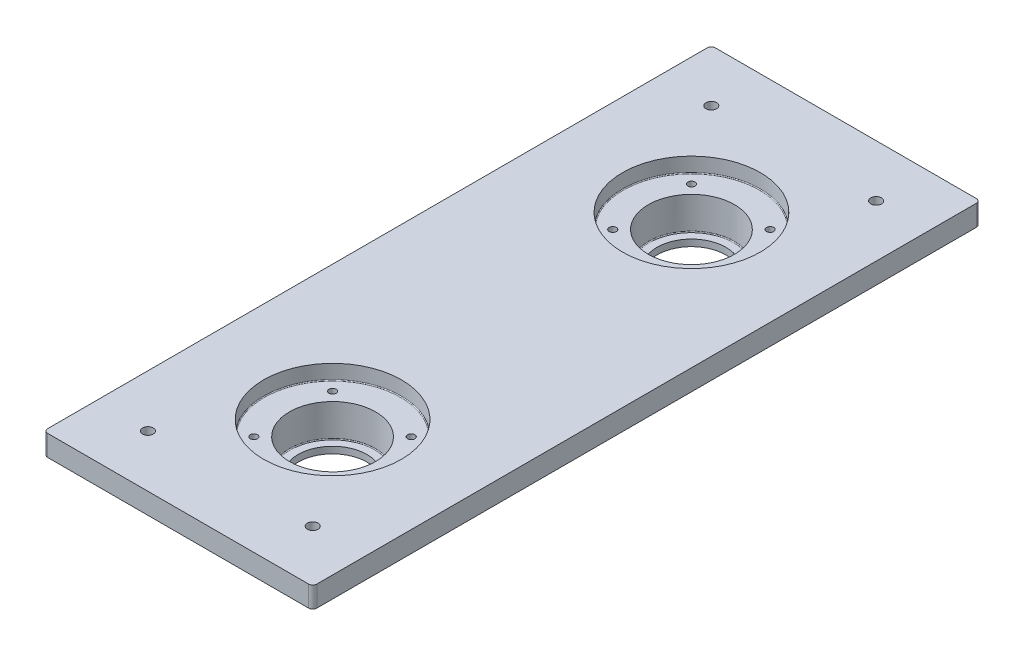
SolidWorks part; units mm, degrees
material "6061-T6 (SS)"
ref_plane "Front" through (0, 0, 0) normal (0, 0, 1) x (1, 0, 0)
ref_plane "Top" through (0, 0, 0) normal (0, 1, 0) x (1, 0, 0)
ref_plane "Right" through (0, 0, 0) normal (1, 0, 0) x (0, 0, -1)
sketch "Sketch1" plane through (0, 0, 0) normal (0, 1, 0) x (1, 0, 0)
  line L0 (64.5, 160) -> (-64.5, -160) construction
  line L1 (-64.5, 160) -> (64.5, 160)
  line L2 (-64.5, 160) -> (-64.5, -160)
  line L3 (-64.5, -160) -> (64.5, -160)
  line L4 (64.5, 160) -> (64.5, -160)
  line L5 (0, 0) -> (0, 92.0872) construction
  circle A0 centre (0, 86) radius 74 construction
  point P4 (0, 0)
  dimension "D3" = 148
  dimension "D1" = 129
  dimension "D2" = 320
extrude "Extrude1" add sketch "Sketch1" along normal blind 10
sketch "Sketch2" plane through (0, 10, 0) normal (0, -1, 0) x (1, 0, 0)
  circle A0 centre (0, -86) radius 23.8188
  dimension "D1" = 47.6377
extrude "Extrude2" add sketch "Sketch2" along normal blind 25.92
sketch "Sketch3" plane through (0, -15.92, 0) normal (0, -1, 0) x (1, 0, 0)
  circle A0 centre (0, -86) radius 16.51
  dimension "D1" = 33.02
extrude "Extrude3" cut sketch "Sketch3" against normal through all
sketch "Sketch4" plane through (0, 10, 0) normal (0, 1, 0) x (1, 0, 0)
  circle A0 centre (0, 86) radius 20.6438
  dimension "D1" = 41.2877
extrude "Extrude4" cut sketch "Sketch4" against normal offset from surface (22.745 mm away) 3.175 up to face at (0, -15.92, -102.51)
sketch "Sketch5" plane through (0, 10, 0) normal (0, 1, 0) x (1, 0, 0)
  circle A0 centre (0, 86) radius 33.02
  dimension "D1" = 66.04
extrude "Extrude5" cut sketch "Sketch5" against normal blind 7.112
sketch "Sketch11" plane through (0, 2.888, 0) normal (0, -1, 0) x (1, 0, 0)
  circle A2 centre (0, -86) radius 23.8189 construction
  circle A3 centre (0, -86) radius 23.8189
  circle A5 centre (0, -86) radius 35.56
  circle A6 centre (0, -86) radius 35.56
  dimension "D1" = 2.54
extrude "Boss-Extrude2" add sketch "Sketch11" along normal blind 8.382
sketch "hole positions" plane through (0, 2.888, 0) normal (0, 1, 0) x (1, 0, 0)
  line L0 (-18.8585, 104.8585) -> (18.8585, 67.1415) construction
  line L1 (-18.8585, 104.8585) -> (18.8585, 104.8585)
  line L2 (-18.8585, 104.8585) -> (-18.8585, 67.1415)
  line L3 (-18.8585, 67.1415) -> (18.8585, 67.1415)
  line L4 (18.8585, 104.8585) -> (18.8585, 67.1415)
  point P4 (0, 86)
  dimension "D1" = 53.34
hole_wizard "#8-32 Tapped Hole1" positions "3DSketch1" profile "Sketch7" tap size "#8-32" standard "Ansi Inch" end condition through all
sketch3d "3DSketch1"
  point P0 (-18.8585, 2.888, -104.8585)
  point P3 (18.8585, 2.888, -104.8585)
  point P6 (18.8585, 2.888, -67.1415)
  point P9 (-18.8585, 2.888, -67.1415)
sketch "Sketch7" plane through (-18.8585, 2.888, -104.8585) normal (1, 0, 0) x (0, 0, 1)
  line L0 (0, 0) -> (0, 18.808)
  line L1 (0, 18.808) -> (1.7272, 18.808)
  line L2 (1.7272, 18.808) -> (1.7272, 0)
  line L5 (1.7272, 0) -> (0, 0)
  line L11 (0, -6.35) -> (0, 107.95) construction
  dimension "Thru Tap Drill Dia." = 3.4544
  dimension "Thru Tap Drill Depth" = 18.808
cosmetic thread "Hole Thread14" parameters "D1"=8.6, "D2"=4.1656
cosmetic thread "Hole Thread15" parameters "D1"=8.6, "D2"=4.1656
cosmetic thread "Hole Thread16" parameters "D1"=8.6, "D2"=4.1656
cosmetic thread "Hole Thread17" parameters "D1"=8.6, "D2"=4.1656
mirror "Mirror1" about plane through (0, 0, 0) normal (0, 0, 1) of "Boss-Extrude2", "Extrude2", "Extrude3", "Extrude4", "Extrude5", "#8-32 Tapped Hole1"
fillet "Fillet1" radius 0.3962 8 edges at (0, 2.888, 52.98) (0, -12.745, 65.3562) (0, -12.745, -106.6439) (0, 2.888, -52.98) (0, -5.494, 62.1812) (0, 0, 121.56) (0, -5.494, -109.8189) (0, 0, -50.44)
fillet "Fillet2" radius 2 4 edges at (-64.5, 5, -160) (64.5, 5, -160) (-64.5, 5, 160) (64.5, 5, 160)
sketch "Sketch8" plane through (0, 10, 0) normal (0, 1, 0) x (1, 0, 0)
  line L0 (62.5, 160) -> (-62.5, 160) construction
  line L1 (-64.5, 158) -> (-64.5, -158) construction
  circle A0 centre (-39.5, 135) radius 25
  dimension "D1" = 50
hole_wizard "1/4-20 Tapped Hole1" positions "Sketch10" profile "Sketch9" tap size "1/4-20" standard "Ansi Inch" end condition through all
sketch "Sketch10" plane through (0, 10, 0) normal (0, 1, 0) x (-1, 0, 0)
  point P0 (39.5, -135)
sketch "Sketch9" plane through (-39.5, 10, -135) normal (1, 0, 0) x (0, 0, 1)
  line L0 (0, 0) -> (0, 25.92)
  line L1 (0, 25.92) -> (2.5527, 25.92)
  line L2 (2.5527, 25.92) -> (2.5527, 0)
  line L5 (2.5527, 0) -> (0, 0)
  line L11 (0, -6.35) -> (0, 107.95) construction
  dimension "Thru Tap Drill Dia." = 5.1054
  dimension "Thru Tap Drill Depth" = 25.92
cosmetic thread "Hole Thread5" parameters "D2"=6.35
mirror "Mirror2" about plane through (0, 0, 0) normal (1, 0, 0) of "1/4-20 Tapped Hole1"
mirror "Mirror3" about plane through (0, 0, 0) normal (0, 0, 1) of "Mirror2", "1/4-20 Tapped Hole1"
